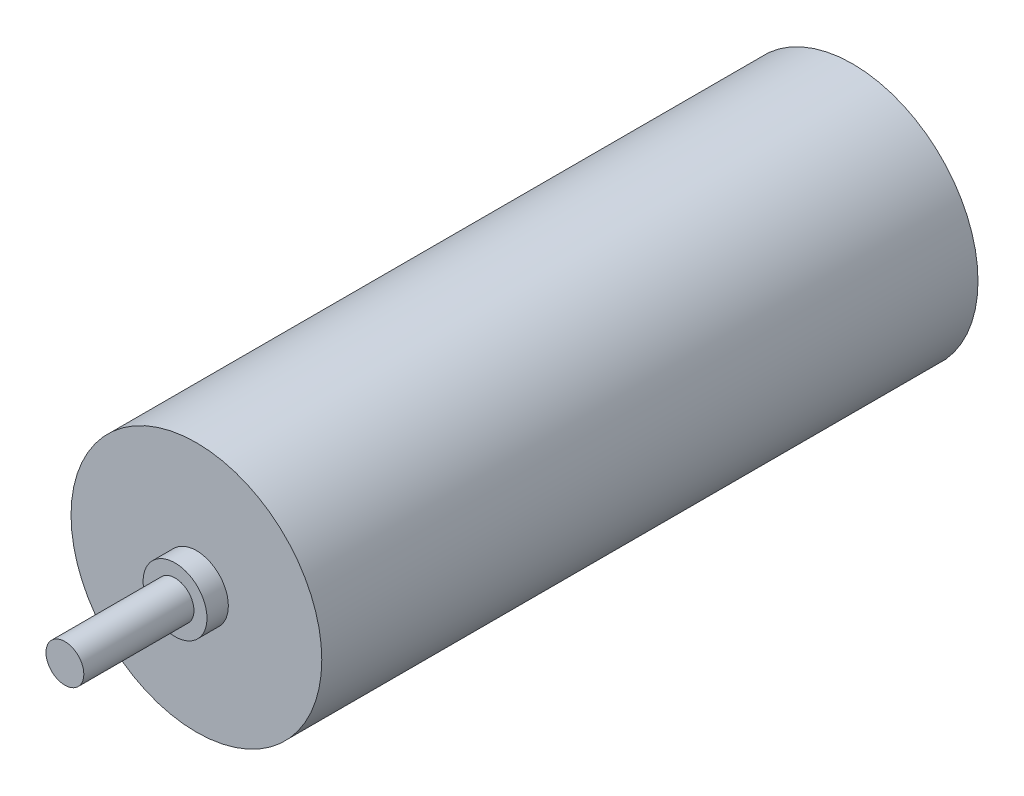
SolidWorks part; units mm, degrees
ref_plane "Front Plane" through (0, 0, 0) normal (0, 0, 1) x (1, 0, 0)
ref_plane "Top Plane" through (0, 0, 0) normal (0, 1, 0) x (1, 0, 0)
ref_plane "Right Plane" through (0, 0, 0) normal (1, 0, 0) x (0, 0, -1)
sketch "Sketch1" plane through (0, 0, 0) normal (0, 0, 1) x (1, 0, 0)
  circle A0 centre (0, 0) radius 13.25
  dimension "D1" = 26.5
extrude "Boss-Extrude1" add sketch "Sketch1" along normal blind 69.35
sketch "Sketch2" plane through (0, 0, 69.35) normal (0, 0, 1) x (1, 0, 0)
  circle A0 centre (0, 0) radius 3.375
  dimension "D1" = 6.75
extrude "Boss-Extrude2" add sketch "Sketch2" along normal blind 2.26
sketch "Sketch3" plane through (0, 0, 71.61) normal (0, 0, 1) x (1, 0, 0)
  circle A0 centre (0, 0) radius 2
  dimension "D1" = 4
extrude "Boss-Extrude3" add sketch "Sketch3" along normal blind 11.64
